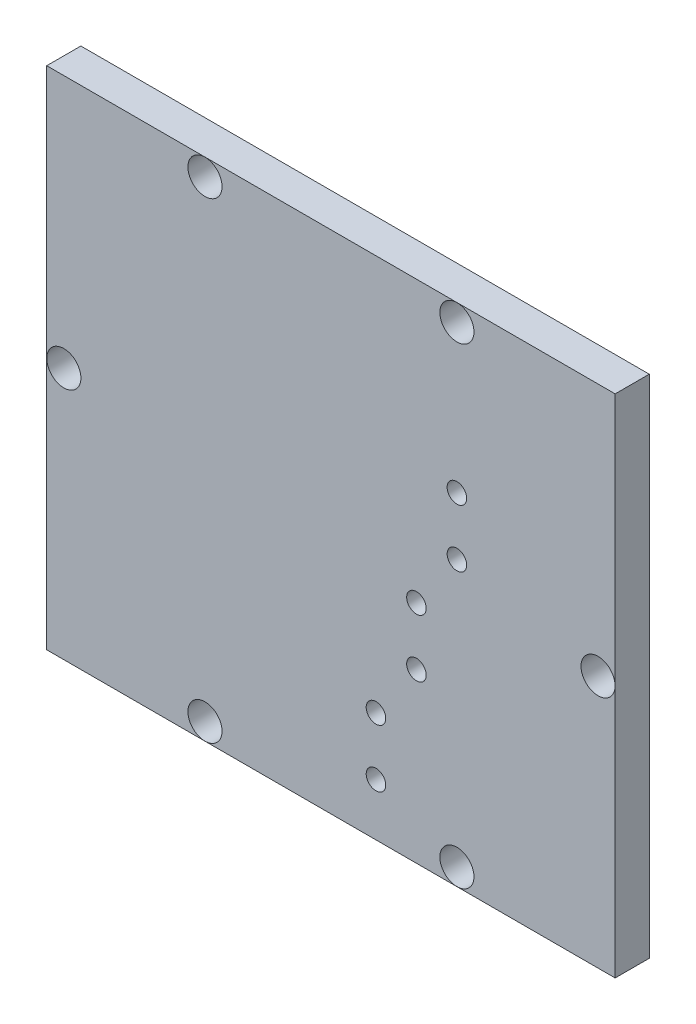
SolidWorks part; units mm, degrees
ref_plane "Front Plane" through (0, 0, 0) normal (0, 0, 1) x (1, 0, 0)
ref_plane "Top Plane" through (0, 0, 0) normal (0, 1, 0) x (1, 0, 0)
ref_plane "Right Plane" through (0, 0, 0) normal (1, 0, 0) x (0, 0, -1)
sketch "Sketch1" plane through (0, 0, 0) normal (0, 0, 1) x (1, 0, 0)
  line L0 (0, 0) -> (0, 141.2875)
  line L1 (0, 141.2875) -> (158.75, 141.2875)
  line L2 (158.75, 141.2875) -> (158.75, 0)
  line L3 (158.75, 0) -> (0, 0)
  dimension "D1" = 141.2875
  dimension "D2" = 158.75
extrude "Boss-Extrude1" add sketch "Sketch1" along normal blind 9.525
sketch "Sketch2" plane through (0, 0, 9.525) normal (0, 0, 1) x (1, 0, 0)
  line L0 (0, 141.2875) -> (0, 0) construction
  line L1 (158.75, 0) -> (158.75, 141.2875) construction
  line L2 (158.75, 141.2875) -> (0, 141.2875) construction
  line L3 (0, 0) -> (158.75, 0) construction
  circle A0 centre (4.7752, 70.5036) radius 4.7625
  circle A1 centre (153.9748, 70.6437) radius 4.7625
  circle A2 centre (44.196, 136.5123) radius 4.7625
  circle A3 centre (114.554, 136.5123) radius 4.7625
  circle A4 centre (44.196, 4.7752) radius 4.7625
  circle A5 centre (114.554, 4.7752) radius 4.7625
  circle A6 centre (91.948, 14.605) radius 2.7305
  circle A7 centre (91.948, 30.734) radius 2.7305
  circle A8 centre (103.251, 46.863) radius 2.7305
  circle A9 centre (103.251, 62.992) radius 2.7305
  circle A10 centre (114.554, 79.121) radius 2.7305
  circle A11 centre (114.554, 95.25) radius 2.7305
  dimension "D1" = 9.525
  dimension "D3" = 9.525
  dimension "D5" = 9.525
  dimension "D8" = 9.525
  dimension "D11" = 9.525
  dimension "D13" = 9.525
  dimension "D14" = 5.461
  dimension "D17" = 5.461
  dimension "D19" = 5.461
  dimension "D22" = 5.461
  dimension "D24" = 5.461
  dimension "D27" = 5.461
  dimension "D2" = 4.7752
  dimension "D4" = 4.7752
  dimension "D6" = 4.7752
  dimension "D7" = 44.196
  dimension "D9" = 4.7752
  dimension "D10" = 44.196
  dimension "D12" = 4.7752
  dimension "D15" = 14.605
  dimension "D16" = 66.802
  dimension "D18" = 16.129
  dimension "D20" = 11.303
  dimension "D21" = 16.129
  dimension "D23" = 16.129
  dimension "D25" = 11.303
  dimension "D26" = 16.129
  dimension "D28" = 16.129
  dimension "D29" = 4.7752
extrude "Cut-Extrude7" cut sketch "Sketch2" against normal blind 9.525
